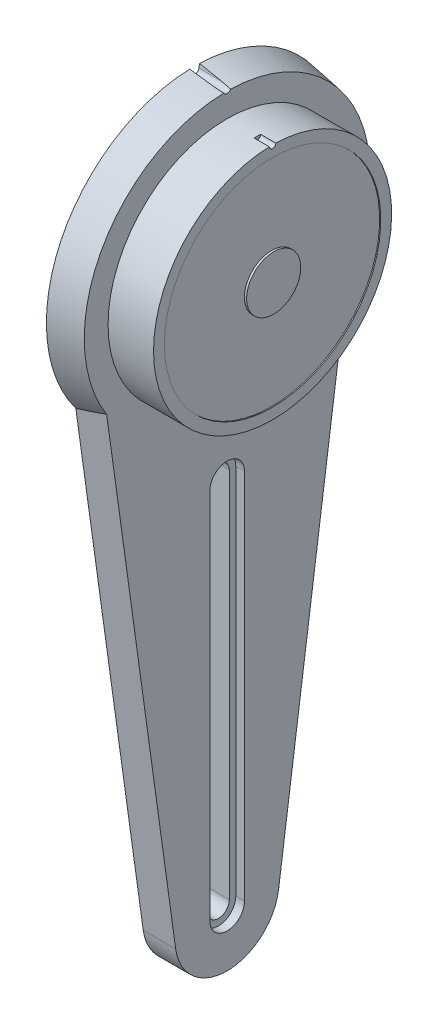
SolidWorks part; units mm, degrees
ref_plane "Face" through (0, 0, 0) normal (0, 0, 1) x (1, 0, 0)
ref_plane "Dessus" through (0, 0, 0) normal (0, 1, 0) x (1, 0, 0)
ref_plane "Droite" through (0, 0, 0) normal (1, 0, 0) x (0, 0, -1)
sketch "Esquisse1" plane through (0, 0, 0) normal (0, 0, 1) x (1, 0, 0)
  line L0 (-40.9669, 0) -> (123.7848, 0) construction
  line L1 (0, 0) -> (0, 34.25)
  line L2 (0, 34.25) -> (7.5, 33)
  line L3 (7.5, 33) -> (7.5, 27.5)
  line L4 (7.5, 27.5) -> (18, 27.5)
  line L5 (18, 27.5) -> (18, 25)
  line L6 (18, 25) -> (17.75, 25)
  line L7 (17.75, 25) -> (17.75, 6.25)
  line L8 (17.75, 6.25) -> (18.25, 6.25)
  line L9 (18.25, 6.25) -> (18.25, 0)
  line L10 (18.25, 0) -> (0, 0)
  dimension "D1" = 68.5
  dimension "D2" = 66
  dimension "D3" = 55
  dimension "D4" = 50
  dimension "D5" = 12.5
  dimension "D6" = 7.5
  dimension "D7" = 10.25
  dimension "D8" = 10.5
  dimension "D9" = 0.5
revolve "Révolution1" add sketch "Esquisse1" angle 360 about L0
sketch "Esquisse2" plane through (18, 0, 0) normal (1, 0, 0) x (0, 0, -1)
  circle A0 centre (0, 27.5) radius 0.75
  dimension "D2" = 1.5
  dimension "D1" = 27.5
extrude "Enlèv. mat.-Extru.1" cut sketch "Esquisse2" against normal blind 3.5
sketch "Esquisse3" plane through (7.5, 0, 0) normal (1, 0, 0) x (0, 0, -1)
  line L0 (-0.9834, 33.3684) -> (-1.9977, 38.8594)
  line L1 (0.9844, 33.374) -> (1.9649, 38.8594)
  line L2 (1.9649, 38.8594) -> (-1.9977, 38.8594)
  arc A0 (-0.9834, 33.3684) -> (0.9844, 33.374) centre (0, 33.55) ccw
  dimension "D1" = 2
  dimension "D2" = 33.55
extrude "Enlèv. mat.-Extru.2" cut sketch "Esquisse3" against normal through all
sketch "Esquisse4" plane through (0, 0, 0) normal (-1, 0, 0) x (0, 0, 1)
  line L0 (29.7155, -4.1221) -> (11.8862, -132.6489)
  line L1 (-29.7155, -4.1221) -> (-11.8862, -132.6489)
  line L2 (0, 0) -> (0, -117.5499) construction
  line L3 (2.5, -45) -> (2.5, -131)
  line L4 (-2.5, -45) -> (-2.5, -131)
  arc A0 (-11.8862, -132.6489) -> (11.8862, -132.6489) centre (0, -131) ccw
  arc A2 (29.7155, -4.1221) -> (-29.7155, -4.1221) centre (0, 0) ccw
  arc A3 (-2.5, -131) -> (2.5, -131) centre (0, -131) ccw
  arc A4 (2.5, -45) -> (-2.5, -45) centre (0, -45) ccw
  dimension "D1" = 12
  dimension "D3" = 60
  dimension "D2" = 131
  dimension "D4" = 45
  dimension "D5" = 2.5
extrude "Extrusion1" add sketch "Esquisse4" against normal blind 7.5
sketch "Esquisse5" plane through (0, 0, 0) normal (-1, 0, 0) x (0, 0, 1)
  line L0 (-11.0398, -106) -> (-6, -106)
  line L1 (-6, -45) -> (-6, -65)
  line L2 (-22.1164, -26.152) -> (-16.7274, -65)
  line L3 (-27.4449, -20.49) -> (-11.8862, -132.6489) construction
  line L4 (0, 0) -> (0, -153.5793) construction
  line L5 (-1, -138.433) -> (-1, -136.9161)
  line L6 (-10.7624, -108) -> (-6, -108)
  line L7 (-13.8142, -86) -> (-6, -86)
  line L8 (-13.5368, -88) -> (-6, -88)
  line L9 (-16.7274, -65) -> (-13.25, -65)
  line L10 (-16.4499, -67) -> (-6, -67)
  line L11 (-1, -34.2354) -> (-1, -39.0839)
  line L13 (-13.25, -65) -> (-13.25, -31.5832)
  line L14 (-11.25, -32.3497) -> (-11.25, -65)
  line L15 (-16.4499, -67) -> (-13.8142, -86)
  line L16 (-6, -67) -> (-6, -86)
  line L17 (-11.25, -65) -> (-6, -65)
  line L18 (-6, -88) -> (-6, -106)
  line L19 (-13.5368, -88) -> (-11.0398, -106)
  line L20 (-6, -108) -> (-6, -131)
  line L21 (-10.7624, -108) -> (-7.4289, -132.0305)
  line L23 (10.7624, -108) -> (7.4289, -132.0305)
  line L24 (6, -108) -> (6, -131)
  line L25 (13.5368, -88) -> (11.0398, -106)
  line L26 (6, -88) -> (6, -106)
  line L27 (11.25, -65) -> (6, -65)
  line L28 (6, -67) -> (6, -86)
  line L29 (16.4499, -67) -> (13.8142, -86)
  line L30 (11.25, -32.3497) -> (11.25, -65)
  line L31 (13.25, -65) -> (13.25, -31.5832)
  line L32 (1, -34.2354) -> (1, -39.0839)
  line L33 (16.4499, -67) -> (6, -67)
  line L34 (16.7274, -65) -> (13.25, -65)
  line L35 (13.5368, -88) -> (6, -88)
  line L36 (13.8142, -86) -> (6, -86)
  line L37 (10.7624, -108) -> (6, -108)
  line L38 (1, -138.433) -> (1, -136.9161)
  line L39 (22.1164, -26.152) -> (16.7274, -65)
  line L40 (6, -45) -> (6, -65)
  line L41 (11.0398, -106) -> (6, -106)
  arc A0 (-22.1164, -26.152) -> (-13.25, -31.5832) centre (0, 0) ccw
  arc A1 (-1, -39.0839) -> (-6, -45) centre (0, -45) ccw
  arc A2 (-6, -131) -> (-1, -136.9161) centre (0, -131) ccw
  arc A3 (-11.25, -32.3497) -> (-1, -34.2354) centre (0, 0) ccw
  arc A4 (-7.4289, -132.0305) -> (-1, -138.433) centre (0, -131) ccw
  arc A5 (-1.1376, 34.2311) -> (-27.4449, -20.49) centre (0, 0) ccw construction
  arc A6 (7.4289, -132.0305) -> (1, -138.433) centre (0, -131) cw
  arc A7 (11.25, -32.3497) -> (1, -34.2354) centre (0, 0) cw
  arc A8 (6, -131) -> (1, -136.9161) centre (0, -131) cw
  arc A9 (1, -39.0839) -> (6, -45) centre (0, -45) cw
  arc A10 (22.1164, -26.152) -> (13.25, -31.5832) centre (0, 0) cw
  dimension "D1" = 12
  dimension "D2" = 12
  dimension "D3" = 2
  dimension "D4" = 2
  dimension "D5" = 23
  dimension "D6" = 4.5
  dimension "D7" = 2
  dimension "D8" = 2
  dimension "D9" = 20
  dimension "D10" = 21
  dimension "D11" = 2
  dimension "D12" = 22.5
extrude "Enlèv. mat.-Extru.3" cut sketch "Esquisse5" against normal blind 3.5 draft 7
sketch "Esquisse6" plane through (7.5, 0, 0) normal (1, 0, 0) x (0, 0, -1)
  line L0 (4, -45) -> (4, -131)
  line L1 (-4, -45) -> (-4, -131)
  arc A0 (4, -45) -> (-4, -45) centre (0, -45) ccw
  arc A1 (-4, -131) -> (4, -131) centre (0, -131) ccw
  dimension "D1" = 8
  dimension "D2" = 8
extrude "Enlèv. mat.-Extru.4" cut sketch "Esquisse6" against normal blind 2
